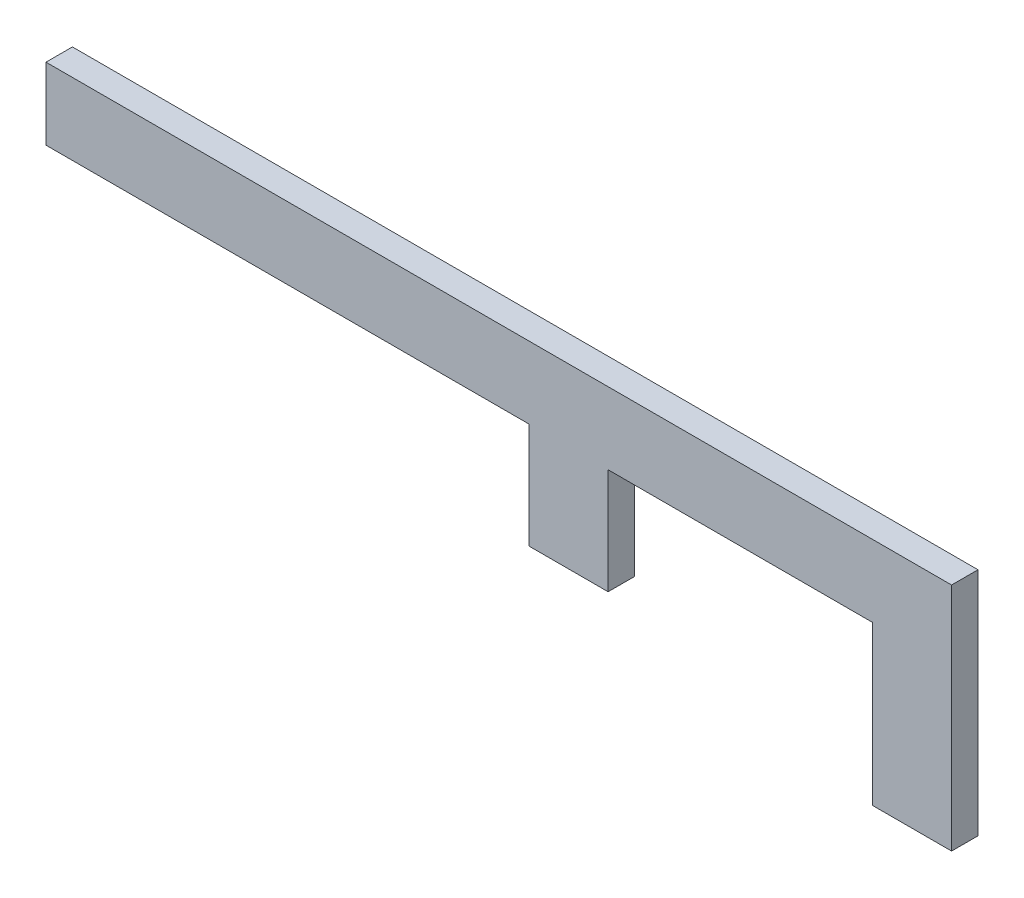
SolidWorks part; units mm, degrees
ref_plane "Front Plane" through (0, 0, 0) normal (0, 0, 1) x (1, 0, 0)
ref_plane "Top Plane" through (0, 0, 0) normal (0, 1, 0) x (1, 0, 0)
ref_plane "Right Plane" through (0, 0, 0) normal (1, 0, 0) x (0, 0, -1)
sketch "Sketch1" plane through (0, 0, 0) normal (0, 0, 1) x (1, 0, 0)
  line L1 (0, 0) -> (257.7544, 0)
  line L2 (-56.7674, -27.2193) -> (-80, -27.2193)
  line L3 (18.4937, -27.2193) -> (257.7544, -27.2193)
  line L4 (257.7544, 0) -> (257.7544, -27.2193)
  line L5 (18.4937, -27.2193) -> (-56.7674, -27.2193)
  line L6 (-80, -27.2193) -> (-85, -27.2193)
  line L7 (0, 0) -> (-70, 0)
  line L9 (-70, 0) -> (-80, 0)
  line L11 (-80, 0) -> (-85, 0)
  line L12 (-85, -27.2193) -> (-85, 0)
  dimension "D1" = 70
  dimension "D2" = 10
  dimension "D3" = 5
extrude "Boss-Extrude1" add sketch "Sketch1" along normal blind 10
sketch "Sketch2" plane through (0, -27.2193, 0) normal (0, -1, 0) x (-1, 0, 0)
  line L0 (85, 0) -> (-257.7544, 0) construction
  line L1 (-257.7544, -10) -> (-227.7544, -10)
  line L2 (-257.7544, -10) -> (-257.7544, 0)
  line L3 (-257.7544, 0) -> (-227.7544, 0)
  line L4 (-227.7544, -10) -> (-227.7544, 0)
  dimension "D1" = 30
extrude "Boss-Extrude2" add sketch "Sketch2" along normal blind 60
sketch "Sketch3" plane through (0, -27.2193, 0) normal (0, -1, 0) x (-1, 0, 0)
  line L0 (85, -10) -> (-227.7544, -10) construction
  line L1 (-127.7544, -10) -> (-97.7544, -10)
  line L2 (-127.7544, -10) -> (-127.7544, 0)
  line L3 (-127.7544, 0) -> (-97.7544, 0)
  line L4 (-97.7544, -10) -> (-97.7544, 0)
  line L5 (85, 0) -> (-227.7544, 0) construction
  line L6 (-227.7544, -10) -> (-227.7544, 0) construction
  dimension "D1" = 30
  dimension "D2" = 100
extrude "Boss-Extrude3" add sketch "Sketch3" along normal blind 40
